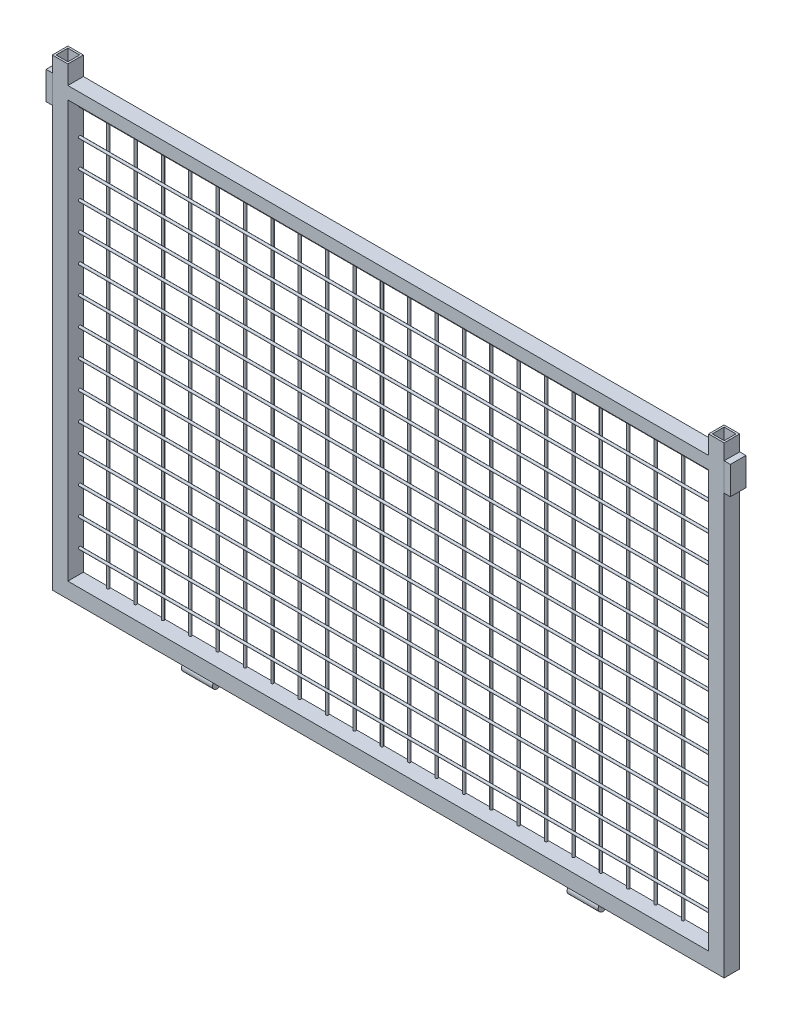
SolidWorks part; units mm, degrees
ref_plane "Piano frontale" through (0, 0, 0) normal (0, 0, 1) x (1, 0, 0)
ref_plane "Piano superiore" through (0, 0, 0) normal (0, 1, 0) x (1, 0, 0)
ref_plane "Piano destro" through (0, 0, 0) normal (1, 0, 0) x (0, 0, -1)
sketch "Schizzo1" plane through (0, 0, 0) normal (0, 1, 0) x (1, 0, 0)
  line L0 (-537, 9.5) -> (-518, 9.5)
  line L1 (-540, -12.5) -> (-515, -12.5)
  line L2 (-540, -12.5) -> (-540, 12.5)
  line L3 (-540, 12.5) -> (-515, 12.5)
  line L4 (-515, -12.5) -> (-515, 12.5)
  line L5 (-518, -9.5) -> (-518, 9.5)
  line L6 (-537, -9.5) -> (-518, -9.5)
  line L7 (-537, -9.5) -> (-537, 9.5)
  line L8 (0, 0) -> (0, 211.96) construction
  line L9 (537, -9.5) -> (537, 9.5)
  line L10 (537, -9.5) -> (518, -9.5)
  line L11 (518, -9.5) -> (518, 9.5)
  line L12 (515, -12.5) -> (515, 12.5)
  line L13 (540, 12.5) -> (515, 12.5)
  line L14 (540, -12.5) -> (540, 12.5)
  line L15 (540, -12.5) -> (515, -12.5)
  line L16 (537, 9.5) -> (518, 9.5)
  point P4 (-515, 0)
  dimension "D1" = 25
  dimension "D2" = 25
  dimension "D3" = 540
  dimension "D4" = 3
extrude "Estrusione-Estrusione1" add sketch "Schizzo1" along normal blind 745
sketch "Schizzo2" plane through (-515, 0, 0) normal (1, 0, 0) x (0, 0, -1)
  line L0 (12.5, 745) -> (12.5, 0) construction
  line L1 (-12.5, 0) -> (12.5, 0)
  line L2 (-12.5, 0) -> (-12.5, 25)
  line L3 (-12.5, 25) -> (12.5, 25)
  line L4 (12.5, 0) -> (12.5, 25)
  line L5 (-9.5, 22) -> (9.5, 22)
  line L6 (9.5, 3) -> (9.5, 22)
  line L7 (-9.5, 3) -> (9.5, 3)
  line L8 (-9.5, 3) -> (-9.5, 22)
  line L9 (-12.5, 372.5) -> (12.5, 372.5) construction
  line L10 (-12.5, 745) -> (-12.5, 0) construction
  line L11 (-9.5, 742) -> (-9.5, 723)
  line L12 (-9.5, 742) -> (9.5, 742)
  line L13 (9.5, 742) -> (9.5, 723)
  line L14 (-9.5, 723) -> (9.5, 723)
  line L15 (12.5, 745) -> (12.5, 720)
  line L16 (-12.5, 720) -> (12.5, 720)
  line L17 (-12.5, 745) -> (-12.5, 720)
  line L18 (-12.5, 745) -> (12.5, 745)
  dimension "D1" = 25
  dimension "D2" = 3
extrude "Estrusione-Estrusione2" add sketch "Schizzo2" along normal up to next (1030 mm away) separate body
ref_plane "Piano1" through (335, 0, 0) normal (1, 0, 0) x (0, 0, -1)
sketch "Schizzo4" plane through (335, 0, 0) normal (1, 0, 0) x (0, 0, -1)
  line L0 (-12.5, 745) -> (-12.5, 0) construction
  line L1 (-12.5, 0) -> (12.5, 0) construction
  circle A0 centre (-2.5, -7.5) radius 7.5
  dimension "D1" = 15
  dimension "D2" = 10
extrude "Estrusione-Estrusione3" add sketch "Schizzo4" against normal blind 50 separate body
mirror "Specchia1" about plane through (0, 0, 0) normal (1, 0, 0) of bodies 105
sketch "Schizzo5" plane through (540, 0, 0) normal (1, 0, 0) x (0, 0, -1)
  line L0 (-12.5, 745) -> (-12.5, 0) construction
  line L1 (-12.5, 720) -> (12.5, 720)
  line L2 (-12.5, 720) -> (-12.5, 675)
  line L3 (-12.5, 675) -> (12.5, 675)
  line L4 (12.5, 720) -> (12.5, 675)
  line L5 (12.5, 745) -> (12.5, 0) construction
  line L6 (-12.5, 745) -> (12.5, 745) construction
  dimension "D1" = 25
  dimension "D2" = 45
extrude "Estrusione-Estrusione4" add sketch "Schizzo5" along normal blind 10 separate body
mirror "Specchia2" about plane through (0, 0, 0) normal (1, 0, 0) of bodies 107
sketch "Schizzo6" plane through (0, 25, 0) normal (0, 1, 0) x (1, 0, 0)
  line L0 (-515, 12.5) -> (-515, -12.5) construction
  line L1 (515, 12.5) -> (-515, 12.5) construction
  line L2 (-473, 10.5) -> (-429, 10.5) construction
  circle A0 centre (-473, 10.5) radius 2
  circle A1 centre (-429, 10.5) radius 2
  circle A2 centre (-385, 10.5) radius 2
  circle A3 centre (-341, 10.5) radius 2
  circle A4 centre (-297, 10.5) radius 2
  circle A5 centre (-253, 10.5) radius 2
  circle A6 centre (-209, 10.5) radius 2
  circle A7 centre (-165, 10.5) radius 2
  circle A8 centre (-121, 10.5) radius 2
  circle A9 centre (-77, 10.5) radius 2
  circle A10 centre (-33, 10.5) radius 2
  circle A11 centre (11, 10.5) radius 2
  circle A12 centre (55, 10.5) radius 2
  circle A13 centre (99, 10.5) radius 2
  circle A14 centre (143, 10.5) radius 2
  circle A15 centre (187, 10.5) radius 2
  circle A16 centre (231, 10.5) radius 2
  circle A17 centre (275, 10.5) radius 2
  circle A18 centre (319, 10.5) radius 2
  circle A19 centre (363, 10.5) radius 2
  circle A20 centre (407, 10.5) radius 2
  circle A21 centre (451, 10.5) radius 2
  circle A22 centre (495, 10.5) radius 2
  dimension "D1" = 4
  dimension "D2" = 42
  dimension "D4" = 44
  dimension "D3" = 23
extrude "Estrusione-Estrusione5" add sketch "Schizzo6" along normal up to next
sketch "Schizzo7" plane through (-515, 0, 0) normal (1, 0, 0) x (0, 0, -1)
  line L1 (8.5, 720) -> (8.5, 25) construction
  line L2 (6.5, 678) -> (6.5, 634) construction
  line L3 (12.5, 720) -> (-12.5, 720) construction
  circle A0 centre (6.5, 678) radius 2
  circle A1 centre (6.5, 634) radius 2
  circle A2 centre (6.5, 590) radius 2
  circle A3 centre (6.5, 546) radius 2
  circle A4 centre (6.5, 502) radius 2
  circle A5 centre (6.5, 458) radius 2
  circle A6 centre (6.5, 414) radius 2
  circle A7 centre (6.5, 370) radius 2
  circle A8 centre (6.5, 326) radius 2
  circle A9 centre (6.5, 282) radius 2
  circle A10 centre (6.5, 238) radius 2
  circle A11 centre (6.5, 194) radius 2
  circle A12 centre (6.5, 150) radius 2
  circle A13 centre (6.5, 106) radius 2
  circle A14 centre (6.5, 62) radius 2
  dimension "D1" = 4
  dimension "D2" = 42
  dimension "D4" = 44
  dimension "D3" = 15
extrude "Estrusione-Estrusione7" add sketch "Schizzo7" along normal up to next separate body
sketch "Schizzo8" plane through (0, 0, -12.5) normal (0, 0, -1) x (-1, 0, 0)
  line L0 (515, 745) -> (515, 0) construction
  line L1 (-515, 745) -> (515, 745)
  line L2 (-515, 745) -> (-515, 725)
  line L3 (-515, 725) -> (515, 725)
  line L4 (515, 745) -> (515, 725)
  dimension "D1" = 20
extrude "Taglio-Estrusione1" cut sketch "Schizzo8" against normal blind 39
sketch "Schizzo9" plane through (515, 0, 0) normal (-1, 0, 0) x (0, 0, 1)
  line L0 (-12.5, 745) -> (-12.5, 0) construction
  line L1 (12.5, 720) -> (-12.5, 720)
  line L2 (12.5, 720) -> (12.5, 695)
  line L3 (12.5, 695) -> (-12.5, 695)
  line L4 (-12.5, 720) -> (-12.5, 695)
  dimension "D1" = 25
extrude "Estrusione-Estrusione8" add sketch "Schizzo9" along normal up to next (1030 mm away)
sketch "Schizzo10" plane through (0, 0, 12.5) normal (0, 0, 1) x (1, 0, 0)
  line L1 (-515, 725) -> (515, 725)
  line L2 (-515, 725) -> (-515, 715)
  line L3 (-515, 715) -> (515, 715)
  line L4 (515, 725) -> (515, 715)
  point P5 (0, 0)
  dimension "D1" = 10
extrude "Taglio-Estrusione2" cut sketch "Schizzo10" against normal through all
